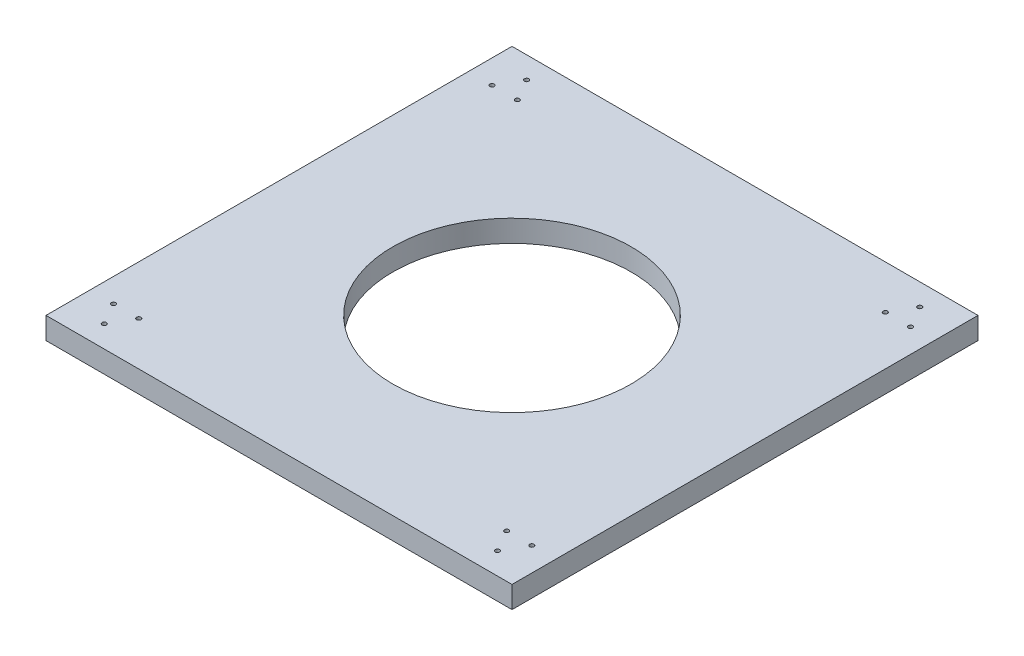
SolidWorks part; units mm, degrees
ref_plane "Front Plane" through (0, 0, 0) normal (0, 0, 1) x (1, 0, 0)
ref_plane "Top Plane" through (0, 0, 0) normal (0, 1, 0) x (1, 0, 0)
ref_plane "Right Plane" through (0, 0, 0) normal (1, 0, 0) x (0, 0, -1)
sketch "Sketch2" plane through (0, 0, 0) normal (0, 1, 0) x (1, 0, 0)
  line L11 (-27.4501, 61.4946) -> (292.5499, 61.4946)
  line L13 (292.5499, 61.4946) -> (292.5499, -258.5054)
  line L15 (-27.4501, -258.5054) -> (292.5499, -258.5054)
  line L17 (-27.4501, 61.4946) -> (-27.4501, -258.5054)
  circle A12 centre (267.5499, 46.4946) radius 1.5
  circle A13 centre (276.2101, 31.4946) radius 1.5
  circle A14 centre (258.8896, 31.4946) radius 1.5
  circle A15 centre (6.2101, 31.4946) radius 1.5
  circle A16 centre (-11.1104, 31.4946) radius 1.5
  circle A17 centre (-2.4501, 46.4946) radius 1.5
  circle A18 centre (-11.1104, -228.5054) radius 1.5
  circle A19 centre (6.2101, -228.5054) radius 1.5
  circle A20 centre (-2.4501, -243.5054) radius 1.5
  circle A21 centre (258.8896, -228.5054) radius 1.5
  circle A22 centre (276.2101, -228.5054) radius 1.5
  circle A23 centre (267.5499, -243.5054) radius 1.5
  circle A24 centre (132.5499, -98.5054) radius 81.7676
  point P41 (130.204, -30.0067)
  dimension "D4" = 270
  dimension "D5" = 260
extrude "Boss-Extrude1" add sketch "Sketch2" along normal blind 15
